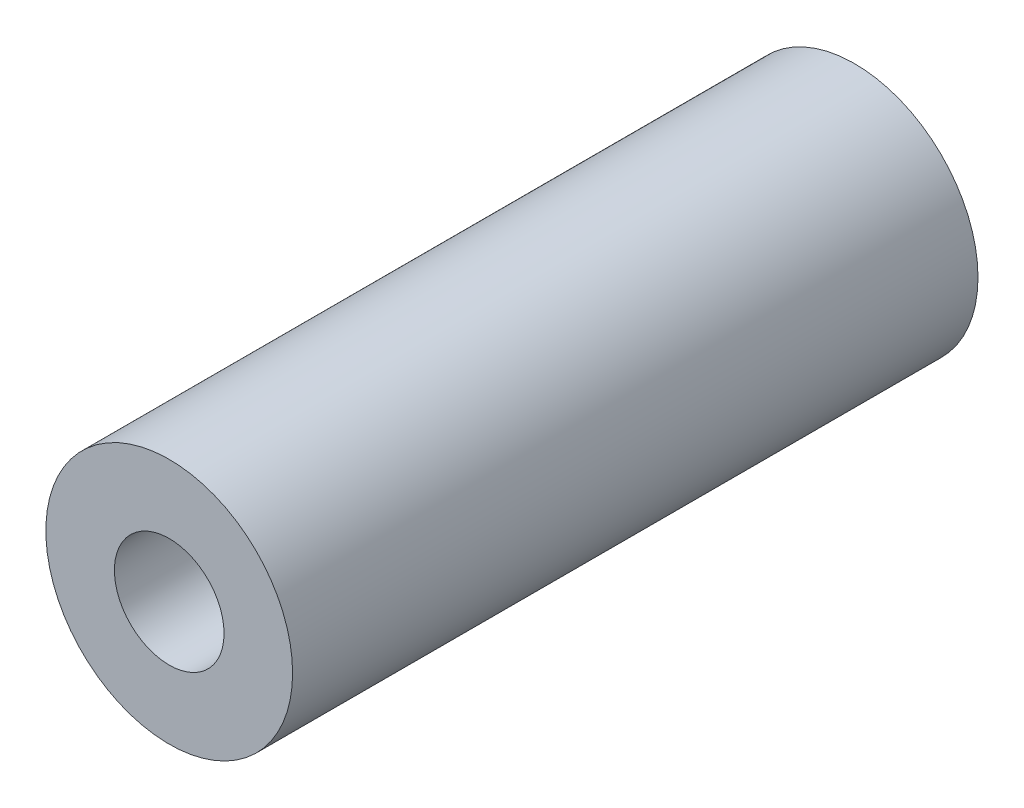
SolidWorks part; units mm, degrees
ref_plane "Ön Düzlem" through (0, 0, 0) normal (0, 0, 1) x (1, 0, 0)
ref_plane "Üst Düzlem" through (0, 0, 0) normal (0, 1, 0) x (1, 0, 0)
ref_plane "Sağ Düzlem" through (0, 0, 0) normal (1, 0, 0) x (0, 0, -1)
sketch "Çizim1" plane through (0, 0, 0) normal (0, 0, 1) x (1, 0, 0)
  circle A0 centre (0, 0) radius 8
  circle A1 centre (0, 0) radius 18
extrude "Yükseklik-Ekstrüzyon1" add sketch "Çizim1" along normal blind 100
